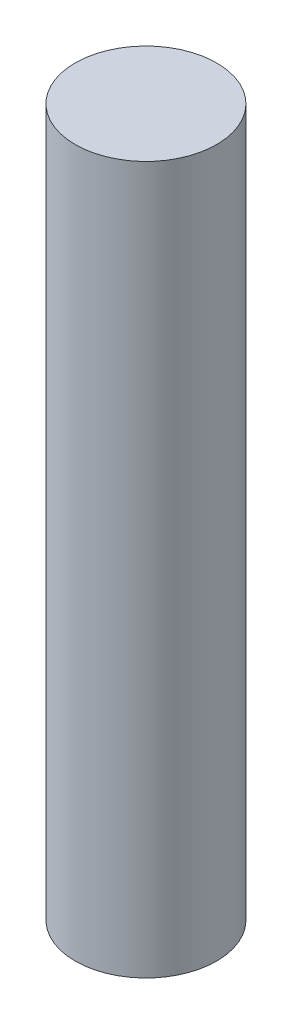
SolidWorks part; units mm, degrees
ref_plane "Front Plane" through (0, 0, 0) normal (0, 0, 1) x (1, 0, 0)
ref_plane "Top Plane" through (0, 0, 0) normal (0, 1, 0) x (1, 0, 0)
ref_plane "Right Plane" through (0, 0, 0) normal (1, 0, 0) x (0, 0, -1)
sketch "Sketch1" plane through (0, 0, 0) normal (0, 1, 0) x (1, 0, 0)
  circle A0 centre (0, 0) radius 3.175
  dimension "D1" = 6.35
extrude "Boss-Extrude1" add sketch "Sketch1" along normal blind 31.75
